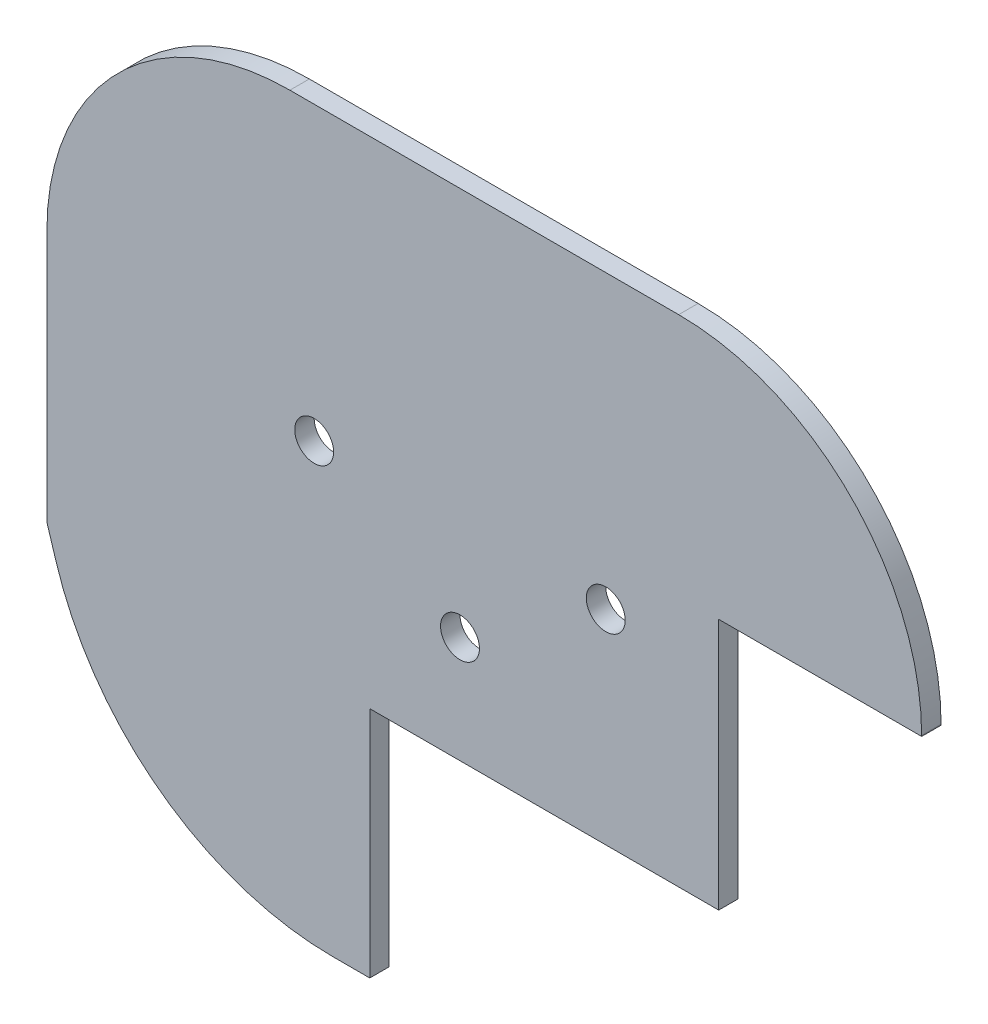
SolidWorks part; units mm, degrees
ref_plane "Front Plane" through (0, 0, 0) normal (0, 0, 1) x (1, 0, 0)
ref_plane "Top Plane" through (0, 0, 0) normal (0, 1, 0) x (1, 0, 0)
ref_plane "Right Plane" through (0, 0, 0) normal (1, 0, 0) x (0, 0, -1)
sketch "Sketch1" plane through (0, 0, 0) normal (0, 0, 1) x (1, 0, 0)
  line L34 (-2.8489, 12.9568) -> (6.3305, 12.9568)
  line L35 (6.3305, 12.9568) -> (7.5911, 12.9568)
  line L36 (7.5911, 12.9568) -> (7.5911, 13)
  line L37 (-4.9089, 25.5) -> (-24.9089, 25.5)
  line L38 (-37.4089, 13) -> (-37.4089, 0)
  line L39 (-37.4089, 0) -> (-36.9355, -1.5212)
  line L40 (-22.7, -12) -> (-20.8, -12)
  line L41 (-20.8, -12) -> (-20.8, 0)
  line L42 (-20.8, 0) -> (-2.8489, 0)
  line L43 (-2.8489, 0) -> (-2.8489, 12.9568)
  line L55 (7.5911, 12.9568) -> (6.3305, 12.9568)
  line L59 (-2.8489, 12.9568) -> (6.3305, 12.9568)
  line L60 (6.3305, 12.9568) -> (7.5911, 12.9568)
  line L61 (7.5911, 12.9568) -> (7.5911, 13)
  line L62 (-4.9089, 25.5) -> (-24.9089, 25.5)
  line L63 (-37.4089, 13) -> (-37.4089, 0)
  line L64 (-37.4089, 0) -> (-36.9355, -1.5212)
  line L65 (-22.7, -12) -> (-20.8, -12)
  line L66 (-20.8, -12) -> (-20.8, 0)
  line L67 (-20.8, 0) -> (-2.8489, 0)
  line L68 (-2.8489, 0) -> (-2.8489, 12.9568)
  arc A24 (7.5911, 13) -> (-4.9089, 25.5) centre (-4.9089, 13) ccw
  arc A25 (-24.9089, 25.5) -> (-37.4089, 13) centre (-24.9089, 13) ccw
  arc A26 (-36.9355, -1.5212) -> (-22.7, -12) centre (-22.7, 2.9089) ccw
  arc A36 (7.5911, 13) -> (-4.9089, 25.5) centre (-4.9089, 13) ccw
  arc A37 (-24.9089, 25.5) -> (-37.4089, 13) centre (-24.9089, 13) ccw
  arc A38 (-36.9355, -1.5212) -> (-22.7, -12) centre (-22.7, 2.9089) ccw
  dimension "D1" = 10.44
  dimension "D2" = 13
extrude "Boss-Extrude1" add sketch "Sketch1" along normal blind 1 contours L39 A26 L40 L41 L42 L43 L34 L35 L36 A24 L37 A25 L38
sketch "Sketch2" plane through (0, 0, 1) normal (0, 0, 1) x (1, 0, 0)
  line L0 (-23.6589, 10.5) -> (-8.6589, 10.5) construction
  line L1 (-16.1589, 5.5) -> (-16.1589, 10.5) construction
  line L2 (-20.8, 0) -> (-2.8489, 0) construction
  line L3 (-2.8489, 0) -> (-2.8489, 12.9568) construction
  circle A0 centre (-8.6589, 10.5) radius 1
  circle A1 centre (-23.6589, 10.5) radius 1
  circle A2 centre (-16.1589, 5.5) radius 1
  dimension "D1" = 2
  dimension "D2" = 15
  dimension "D3" = 5
  dimension "D4" = 5.5
  dimension "D5" = 13.31
extrude "Cut-Extrude1" cut sketch "Sketch2" against normal through all
sketch "Sketch3" plane through (0, 0, 1) normal (0, 0, 1) x (1, 0, 0)
  line L0 (-23.6589, 10.5) -> (-8.6589, 10.5) construction
  line L1 (-16.1589, 5.5) -> (-16.1589, 10.5) construction
  circle A0 centre (-8.6589, 10.5) radius 2.25
  circle A1 centre (-23.6589, 10.5) radius 2.25
  circle A2 centre (-16.1589, 5.5) radius 1 construction
  circle A3 centre (-16.1589, 5.5) radius 2.25
  circle A4 centre (-16.1589, 5.5) radius 1
  dimension "D1" = 4.5
  dimension "D2" = 15
  dimension "D3" = 5
sketch "Sketch5" plane through (0, 0, 0) normal (0, 0, -1) x (-1, 0, 0)
  line L0 (24.9089, 24.05) -> (4.9089, 24.05)
  line L1 (2.8489, 12.9568) -> (-4.7806, 12.9568) construction
  line L2 (-5.0038, 15.8118) -> (-4.6082, 13.1568)
  line L3 (3.3929, 13.1568) -> (-4.6082, 13.1568)
  line L4 (3.2083, 13.1568) -> (-4.6082, 13.1568) construction
  line L5 (29.3704, 8.7076) -> (29.4724, 1.915)
  line L6 (22.7001, -4.3749) -> (21.8, -4.3749)
  line L7 (21.8, -4.3749) -> (21.8, -10.55)
  line L8 (21.8, -10.55) -> (22.7, -10.55)
  line L9 (35.2618, -1.5336) -> (35.4558, -1.389)
  line L10 (35.9589, 1.5439) -> (35.9589, 13)
  line L12 (29.1589, 6.0063) -> (29.1589, 10.2151) construction
  line L13 (29.1589, 6.0063) -> (29.1589, 10.2151) construction
  line L14 (29.3589, 6.0063) -> (29.3589, 10.2151)
  line L15 (2.8489, 12.9568) -> (1.5258, 10.8238) construction
  line L16 (3.2083, 13.1568) -> (2.7524, 12.4219) construction
  line L23 (24.9089, 24.25) -> (4.9089, 24.25) construction
  line L24 (36.1589, 1.5439) -> (36.1589, 13) construction
  line L25 (35.4311, -1.6568) -> (35.6238, -1.5132) construction
  line L26 (21.6, -10.75) -> (22.7, -10.75) construction
  line L27 (21.6, -4.1749) -> (21.6, -10.75) construction
  line L28 (22.7001, -4.1749) -> (21.6, -4.1749) construction
  line L29 (29.1704, 8.7081) -> (29.2723, 1.9166) construction
  line L39 (-5.2016, 15.7823) -> (-4.7806, 12.9568) construction
  arc A0 (-4.223, 19.2219) -> (4.9089, 24.05) centre (4.9089, 13) cw
  arc A1 (-5.0038, 15.8118) -> (-4.223, 19.2219) centre (-0.2562, 16.5192) cw
  arc A4 (6.5188, 15.6904) -> (3.1, 10.947) centre (8.1, 10.947) ccw construction
  arc A5 (29.4724, 1.915) -> (25.7906, -3.6867) centre (23.075, 2.1089) cw
  arc A6 (25.7906, -3.6867) -> (22.7001, -4.3749) centre (22.7002, 2.9088) cw
  arc A7 (35.2618, -1.5336) -> (22.7, -10.55) centre (22.7, 2.7089) cw
  arc A8 (35.9589, 1.5439) -> (35.4558, -1.389) centre (27.1589, 1.5439) cw
  arc A9 (24.9089, 24.05) -> (35.9589, 13) centre (24.9089, 13) cw
  arc A10 (24.8881, 15.9605) -> (6.5188, 15.6904) centre (16.1294, -13.141) ccw construction
  arc A11 (29.1589, 10.2151) -> (24.8881, 15.9605) centre (23.1589, 10.2151) ccw construction
  arc A12 (6.5188, 15.6904) -> (3.1, 10.947) centre (8.1, 10.947) ccw construction
  arc A13 (-5.2016, 15.7823) -> (-4.3882, 19.3345) centre (-0.2562, 16.5192) cw construction
  arc A14 (-4.3882, 19.3345) -> (4.9089, 24.25) centre (4.9089, 13) cw construction
  arc A15 (24.9089, 24.25) -> (36.1589, 13) centre (24.9089, 13) cw construction
  arc A16 (36.1589, 1.5439) -> (35.6238, -1.5132) centre (27.1589, 1.5439) cw construction
  arc A17 (35.4311, -1.6568) -> (22.7, -10.75) centre (22.7, 2.7089) cw construction
  arc A18 (25.7058, -3.5056) -> (22.7001, -4.1749) centre (22.7002, 2.9088) cw construction
  arc A19 (29.2723, 1.9166) -> (25.7058, -3.5056) centre (23.075, 2.1089) cw construction
  arc A20 (24.8881, 15.9605) -> (6.5188, 15.6904) centre (16.1294, -13.141) ccw construction
  arc A21 (29.1589, 10.2151) -> (24.8881, 15.9605) centre (23.1589, 10.2151) ccw construction
  arc A22 (29.3589, 10.2151) -> (24.9457, 16.1521) centre (23.1589, 10.2151) ccw
  arc A23 (2.7524, 12.4219) -> (3.569, 12.9296) centre (6.1868, 7.8086) cw construction
  arc A24 (3.569, 12.9296) -> (27.9884, 12.3496) centre (15.5129, 1.4487) cw construction
  arc A25 (27.9884, 12.3496) -> (29.3704, 8.7076) centre (24.1627, 8.8146) cw construction
  arc A26 (3.6898, 12.7666) -> (27.8396, 12.2159) centre (15.5129, 1.4487) cw construction
  arc A27 (27.8396, 12.2159) -> (29.1704, 8.7081) centre (24.1627, 8.8146) cw construction
  arc A28 (1.5258, 10.8238) -> (3.6898, 12.7666) centre (6.1868, 7.8086) cw construction
  arc A29 (24.9457, 16.1521) -> (6.4556, 15.8801) centre (16.1294, -13.141) ccw
  arc A30 (6.4556, 15.8801) -> (3.3929, 13.1568) centre (8.1, 10.947) ccw
  arc A31 (6.4556, 15.8801) -> (2.9, 10.947) centre (8.1, 10.947) ccw construction
  dimension "D1" = 0.2
  dimension "D2" = 0.2
ref_plane "Plane1" through (-29.1589, 10.2151, -6.5) normal (0, 1, 0) x (1, 0, 0)
sketch "Sketch8" plane through (0, 0, 1) normal (0, 0, 1) x (1, 0, 0)
  line L0 (2.85, 0) -> (3.5669, 17.9927) construction
  line L1 (-2.85, 0) -> (2.85, 0) construction
  line L2 (-29.1589, 10.2022) -> (-29.1589, 6.0063) construction
  line L3 (-21.6, -4.1748) -> (-21.6, -10.75) construction
  line L4 (-21.6, -10.75) -> (-22.7, -10.75) construction
  line L5 (-35.578, -1.6433) -> (-35.6443, -1.4556) construction
  line L6 (-36.1589, 1.5439) -> (-36.1589, 13) construction
  line L7 (-24.9089, 24.25) -> (-4.9089, 24.25) construction
  line L8 (-36.9572, -1.4514) -> (-36.9355, -1.5212) construction
  line L9 (-2.85, 0) -> (-2.85, 10.9354) construction
  line L10 (2.6578, 0.2) -> (3.367, 18.0006)
  line L11 (-24.9089, 24.05) -> (-4.9089, 24.05)
  line L12 (-35.9589, 1.5439) -> (-35.9589, 13)
  line L13 (-35.3894, -1.5767) -> (-35.4558, -1.389)
  line L14 (-21.8, -10.55) -> (-22.7, -10.55)
  line L15 (-21.8, -4.3222) -> (-21.8, -10.55)
  line L16 (-29.3589, 10.2022) -> (-29.3589, 6.0063)
  line L17 (-2.65, 0.2) -> (-2.65, 10.9354)
  line L18 (-2.65, 0.2) -> (2.6578, 0.2)
  line L19 (-36.7662, -1.3919) -> (-36.7445, -1.4617)
  arc A0 (3.367, 18.0006) -> (1.2433, 22.179) centre (-1.4292, 18.1917) ccw
  arc A1 (-29.1589, 6.0063) -> (-21.6, -4.1748) centre (-18.523, 6.0063) ccw construction
  arc A2 (-35.578, -1.6433) -> (-22.7, -10.75) centre (-22.7, 2.9089) ccw construction
  arc A3 (-36.1589, 1.5439) -> (-35.6443, -1.4556) centre (-27.1589, 1.5439) ccw construction
  arc A4 (-24.9089, 24.25) -> (-36.1589, 13) centre (-24.9089, 13) ccw construction
  arc A5 (1.3546, 22.3451) -> (-4.9089, 24.25) centre (-4.9089, 13) ccw construction
  arc A6 (3.5669, 17.9927) -> (1.3546, 22.3451) centre (-1.4292, 18.1917) ccw construction
  arc A7 (-2.85, 10.9354) -> (-6.2787, 15.6821) centre (-7.85, 10.9354) ccw construction
  arc A8 (-6.2787, 15.6821) -> (-24.8795, 15.9502) centre (-16.0044, -13.6987) ccw construction
  arc A9 (-24.8795, 15.9502) -> (-29.1589, 10.2022) centre (-23.1589, 10.2022) ccw construction
  arc A11 (1.2433, 22.179) -> (-4.9089, 24.05) centre (-4.9089, 13) ccw
  arc A12 (-24.9089, 24.05) -> (-35.9589, 13) centre (-24.9089, 13) ccw
  arc A13 (-35.9589, 1.5439) -> (-35.4558, -1.389) centre (-27.1589, 1.5439) ccw
  arc A14 (-35.3894, -1.5767) -> (-22.7, -10.55) centre (-22.7, 2.9089) ccw
  arc A15 (-29.3589, 6.0063) -> (-21.8, -4.3222) centre (-18.523, 6.0063) ccw
  arc A16 (-24.9368, 16.1418) -> (-29.3589, 10.2022) centre (-23.1589, 10.2022) ccw
  arc A17 (-6.2159, 15.872) -> (-24.9368, 16.1418) centre (-16.0044, -13.6987) ccw
  arc A18 (-2.65, 10.9354) -> (-6.2159, 15.872) centre (-7.85, 10.9354) ccw
  line M9 (-2.8489, 0) -> (-2.8489, 12.9568)
  line M10 (-2.8489, 12.9568) -> (7.5911, 12.9568)
  dimension "D1" = 0.2
extrude "Boss-Extrude3" add sketch "Sketch8" against normal blind 2 contours A18 L10 A0 A11 L11 A12 L12 A13 L13 A14 L14 L15 A15 L16 A16 A17 M9 M10
